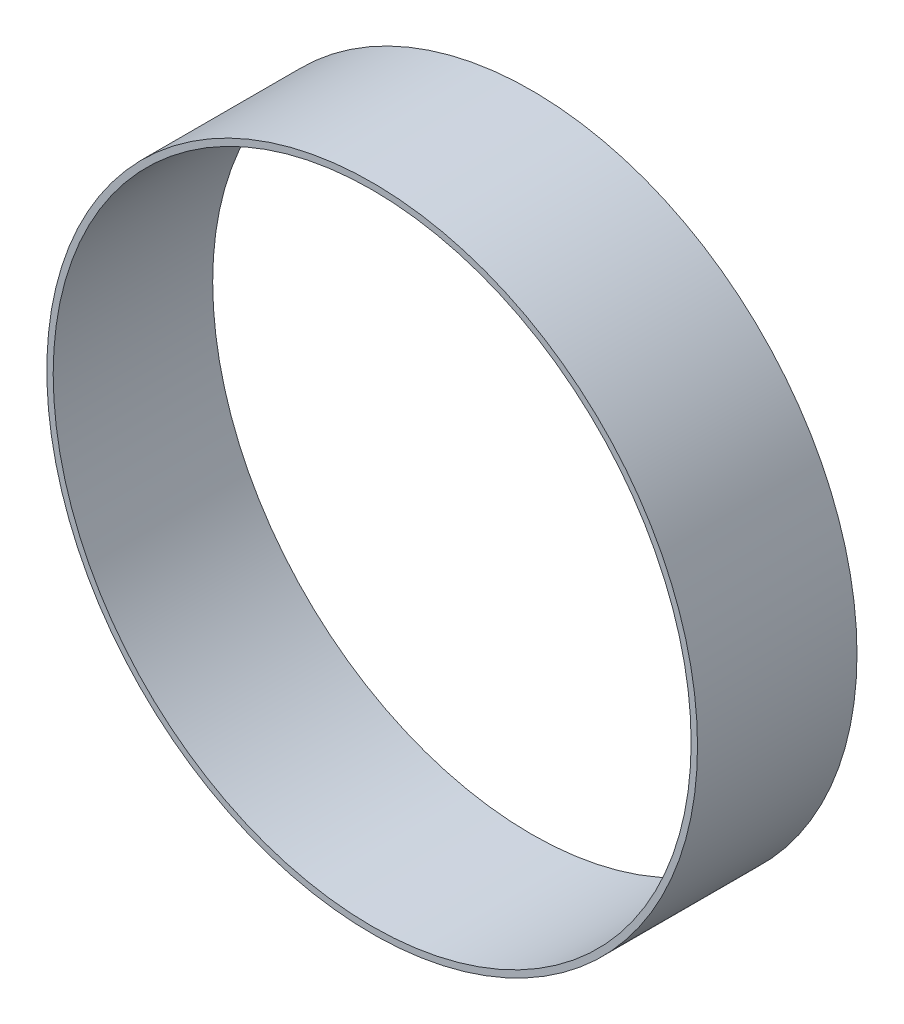
SolidWorks part; units mm, degrees
ref_plane "Front Plane" through (0, 0, 0) normal (0, 0, 1) x (1, 0, 0)
ref_plane "Top Plane" through (0, 0, 0) normal (0, 1, 0) x (1, 0, 0)
ref_plane "Right Plane" through (0, 0, 0) normal (1, 0, 0) x (0, 0, -1)
sketch "Sketch2" plane through (0, 0, 0) normal (0, 0, 1) x (1, 0, 0)
  circle A0 centre (0, 0) radius 51
  circle A1 centre (0, 0) radius 50
  dimension "D1" = 100
  dimension "D2" = 102
extrude "Boss-Extrude1" add sketch "Sketch2" along normal blind 25
